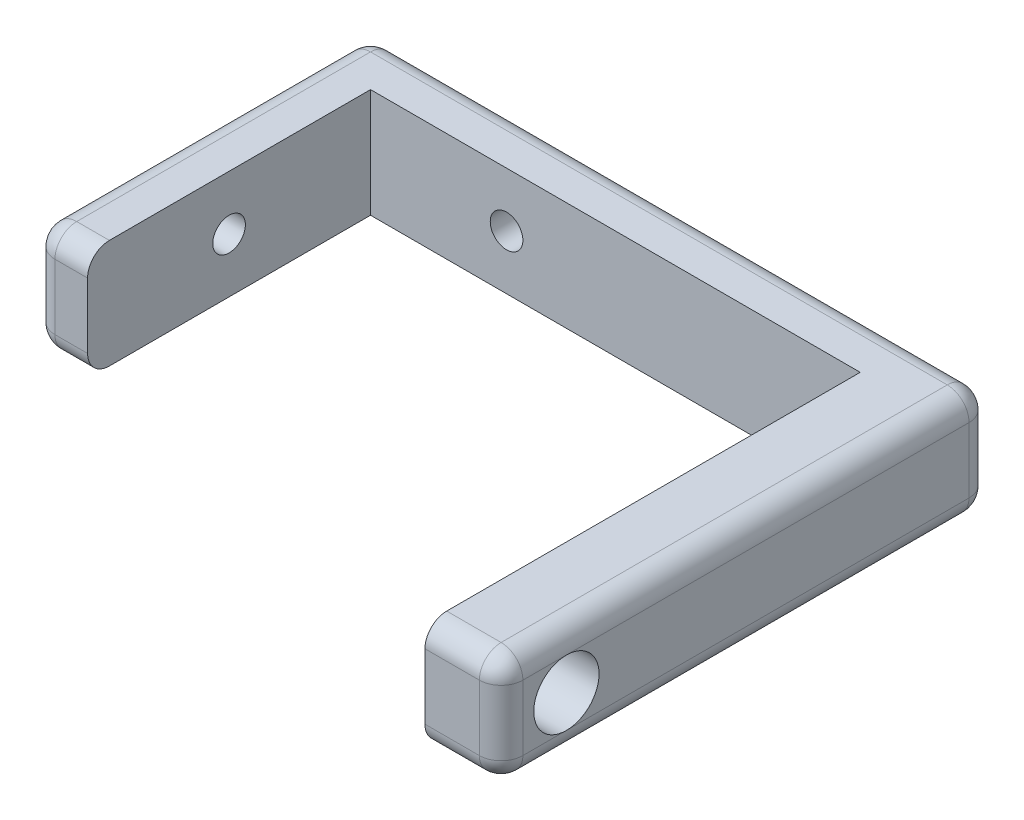
SolidWorks part; units mm, degrees
ref_plane "Front Plane" through (0, 0, 0) normal (0, 0, 1) x (1, 0, 0)
ref_plane "Top Plane" through (0, 0, 0) normal (0, 1, 0) x (1, 0, 0)
ref_plane "Right Plane" through (0, 0, 0) normal (1, 0, 0) x (0, 0, -1)
sketch "Sketch2" plane through (0, 0, 0) normal (0, 1, 0) x (1, 0, 0)
  line L0 (-13, -13) -> (-18, -13)
  line L1 (-13, -13) -> (13, -13)
  line L2 (-13, -13) -> (-13, 13)
  line L3 (-13, 13) -> (13, 13)
  line L4 (13, -13) -> (13, 13)
  line L5 (-13, -13) -> (13, 13) construction
  line L6 (-13, 13) -> (13, -13) construction
  line L7 (-18, -13) -> (-18, 18)
  line L8 (-18, 18) -> (39, 18)
  line L9 (32, 13) -> (32, -27)
  line L10 (13, 13) -> (32, 13)
  line L11 (32, -27) -> (39, -27)
  line L12 (39, -27) -> (39, 18)
  point P0 (0, 0)
  dimension "D1" = 26
  dimension "26" = 26
  dimension "D2" = 5
  dimension "5" = 5
  dimension "D3" = 7
  dimension "D4" = 19
  dimension "40" = 40
extrude "Boss-Extrude1" add sketch "Sketch2" along normal blind 10 contours L11 L12 L8 L7 L0 L2 L3 L10 L9
sketch "Sketch3" plane through (39, 0, 0) normal (1, 0, 0) x (0, 0, -1)
  line L0 (-27, 5) -> (18, 5) construction
  line L1 (-27, 10) -> (-27, 0) construction
  line L2 (18, 10) -> (18, 0) construction
  line L3 (13, 10) -> (13, 0) construction
  line L6 (-27, 10) -> (18, 10) construction
  line L7 (-27, 0) -> (18, 0) construction
  circle A0 centre (-21, 5) radius 3
  dimension "6" = 6
  dimension "5" = 5
  dimension "34" = 34
extrude "Cut-Extrude1" cut sketch "Sketch3" against normal blind 10
fillet "Fillet3" radius 2 14 edges at (-18, 5, -18) (-18, 0, -2.5) (10.5, 0, -18) (39, 0, 4.5) (-18, 10, -2.5) (10.5, 10, -18) (39, 10, 4.5) (39, 5, -18) (39, 5, 27) (-18, 5, 13) (35.5, 10, 27) (35.5, 0, 27) (-15.5, 0, 13) (-15.5, 10, 13)
sketch "Sketch4" plane through (0, 0, -18) normal (0, 0, -1) x (-1, 0, 0)
  line L0 (-15, 8) -> (-15, 2) construction
  line L1 (16, 8) -> (-37, 8) construction
  line L2 (-37, 2) -> (16, 2) construction
  line L3 (16, 2) -> (16, 8) construction
  line L4 (-15, 5) -> (16, 5) construction
  circle A0 centre (0.5, 5) radius 1.5
  point P12 (5.3143, 5)
  point P13 (0, 0)
  dimension "D2" = 3
  dimension "D1" = 31
extrude "Cut-Extrude2" cut sketch "Sketch4" against normal blind 10
sketch "Sketch5" plane through (-18, 0, 0) normal (-1, 0, 0) x (0, 0, 1)
  line L0 (-13, 8) -> (-13, 2) construction
  line L1 (11, 8) -> (-16, 8) construction
  line L2 (-16, 2) -> (11, 2) construction
  line L3 (-18, 2) -> (-18, 8) construction
  line L4 (13, 8) -> (13, 2) construction
  line L5 (-13, 5) -> (13, 5) construction
  circle A0 centre (0, 5) radius 1.5
  dimension "D3" = 3
  dimension "D1" = 5
  dimension "D2" = 26
extrude "Cut-Extrude3" cut sketch "Sketch5" against normal blind 10
